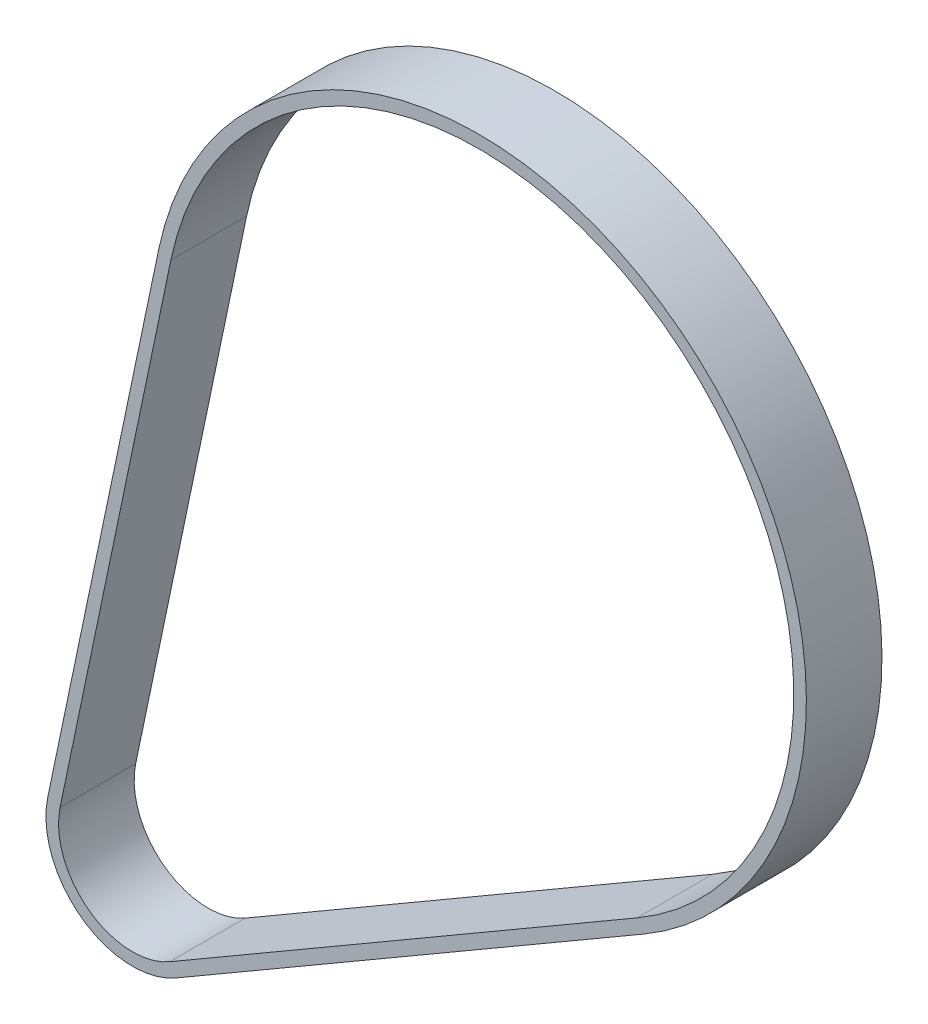
SolidWorks part; units mm, degrees
ref_plane "Front Plane" through (0, 0, 0) normal (0, 0, 1) x (1, 0, 0)
ref_plane "Top Plane" through (0, 0, 0) normal (0, 1, 0) x (1, 0, 0)
ref_plane "Right Plane" through (0, 0, 0) normal (1, 0, 0) x (0, 0, -1)
sketch "Sketch2" plane through (0, 0, 0) normal (0, 0, 1) x (1, 0, 0)
  line L0 (0, 0) -> (1, 0) construction
  line L1 (0, 0) -> (0, 1) construction
  line L2 (4.8036, 42.462) -> (-32.2943, 20.8981)
  line L3 (-41.7295, 27.7099) -> (-32.9371, 69.7093)
  arc A0 (-32.9371, 69.7093) -> (4.8036, 42.462) centre (-8, 64.4888) cw
  arc A1 (-32.2943, 20.8981) -> (-41.7295, 27.7099) centre (-35.4952, 26.4048) cw
extrude "Extrude-Thin1" add sketch "Sketch2" along normal blind 3 and the other way blind 3 thin thin type two direction wall 0.5 second wall 0.5
